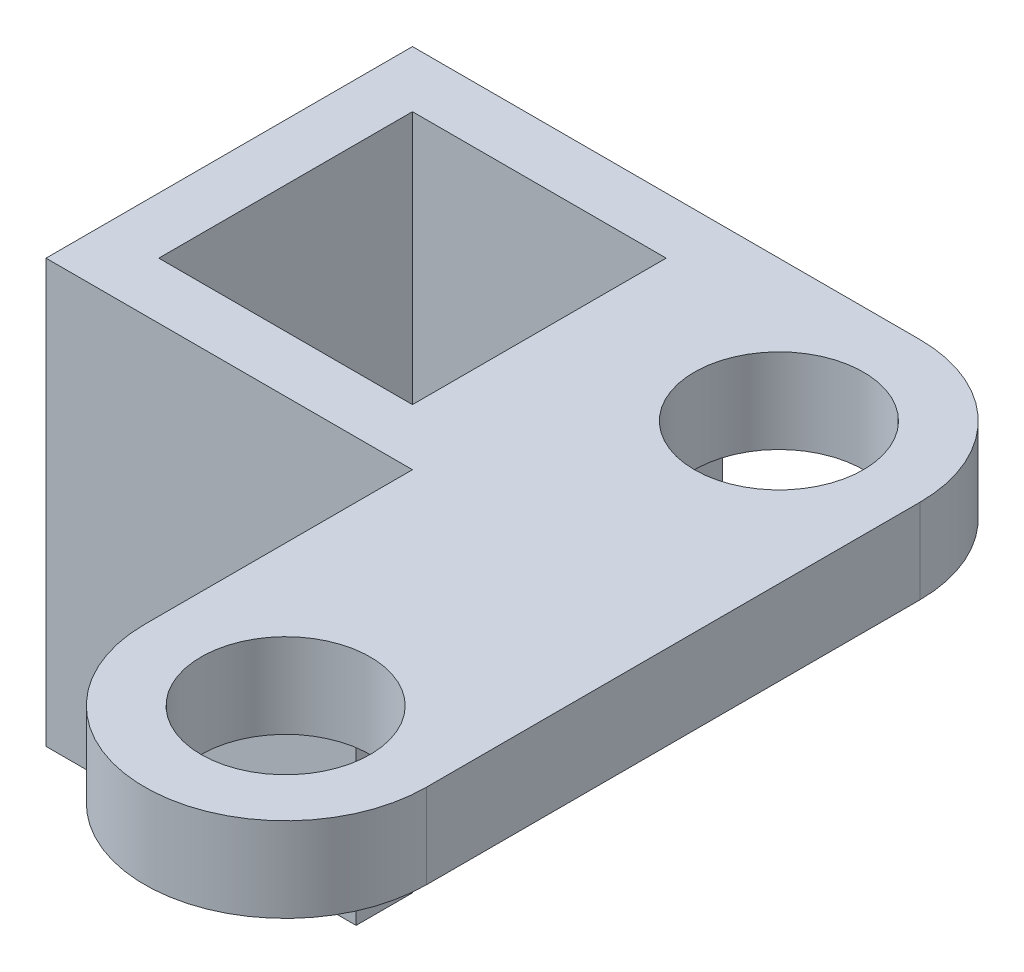
SolidWorks part; units mm, degrees
ref_plane "Front Plane" through (0, 0, 0) normal (0, 0, 1) x (1, 0, 0)
ref_plane "Top Plane" through (0, 0, 0) normal (0, 1, 0) x (1, 0, 0)
ref_plane "Right Plane" through (0, 0, 0) normal (1, 0, 0) x (0, 0, -1)
sketch "Sketch1" plane through (0, 0, 0) normal (0, 1, 0) x (1, 0, 0)
  line L0 (-3.2697, -7.8457) -> (-3.2697, 9.6543)
  line L1 (6.7303, 9.6543) -> (6.7303, -7.8457)
  line L2 (1.7303, 9.6543) -> (1.7303, -7.8457) construction
  line L3 (-3.2697, 9.6543) -> (6.7303, 9.6543) construction
  line L4 (6.7303, -7.8457) -> (-3.2697, -7.8457) construction
  circle A1 centre (1.7303, -7.8457) radius 3
  arc A2 (-3.2697, 9.6543) -> (6.7303, 9.6543) centre (1.7303, 9.6543) cw
  arc A3 (6.7303, -7.8457) -> (-3.2697, -7.8457) centre (1.7303, -7.8457) cw
  dimension "D2" = 6
  dimension "D4" = 5
  dimension "D3" = 17.5
  dimension "D5" = 0
extrude "Boss-Extrude1" add sketch "Sketch1" along normal blind 3
sketch "Sketch2" plane through (0, 3, 0) normal (0, 1, 0) x (1, 0, 0)
  circle A0 centre (1.7303, 9.6543) radius 3
  dimension "D1" = 6
extrude "Cut-Extrude1" cut sketch "Sketch2" against normal blind 3
sketch "Sketch3" plane through (0, 0, 0) normal (0, -1, 0) x (-1, 0, 0)
  line L0 (-1.7303, 14.6543) -> (16.2697, 14.6543)
  line L1 (16.2697, 14.6543) -> (16.2697, 1.6543)
  line L2 (16.2697, 1.6543) -> (3.2697, 1.6543)
  line L3 (3.2697, 9.6543) -> (3.2697, -7.8457) construction
  line L4 (3.2697, 1.6543) -> (16.2697, 14.6543) construction
  line L5 (3.2697, 1.6543) -> (3.2697, 9.6543)
  line L6 (5.2697, 3.6543) -> (14.2697, 3.6543)
  line L7 (5.2697, 3.6543) -> (5.2697, 12.6543)
  line L8 (5.2697, 12.6543) -> (14.2697, 12.6543)
  line L9 (14.2697, 3.6543) -> (14.2697, 12.6543)
  line L10 (5.2697, 3.6543) -> (14.2697, 12.6543) construction
  line L11 (5.2697, 12.6543) -> (14.2697, 3.6543) construction
  arc A0 (3.2697, 9.6543) -> (-6.7303, 9.6543) centre (-1.7303, 9.6543) ccw construction
  arc A1 (3.2697, 9.6543) -> (-1.7303, 14.6543) centre (-1.7303, 9.6543) ccw
  point P9 (9.7697, 8.1543)
  dimension "D1" = 13
  dimension "D2" = 13
  dimension "D3" = 9
extrude "Boss-Extrude2" add sketch "Sketch3" against normal blind 3
sketch "Sketch4" plane through (0, 0, 0) normal (0, -1, 0) x (-1, 0, 0)
  line L0 (5.2697, 12.6543) -> (5.2697, 14.6543)
  line L1 (16.2697, 14.6543) -> (-1.7303, 14.6543) construction
  line L2 (5.2697, 14.6543) -> (16.2697, 14.6543)
  line L3 (16.2697, 14.6543) -> (16.2697, 1.6543)
  line L4 (16.2697, 1.6543) -> (5.2697, 1.6543)
  line L5 (3.2697, 1.6543) -> (16.2697, 1.6543) construction
  line L6 (5.2697, 1.6543) -> (5.2697, 3.6543)
  line L7 (5.2697, 3.6543) -> (14.2697, 3.6543)
  line L8 (14.2697, 3.6543) -> (14.2697, 12.6543)
  line L9 (14.2697, 12.6543) -> (5.2697, 12.6543)
extrude "Boss-Extrude3" add sketch "Sketch4" along normal blind 12
